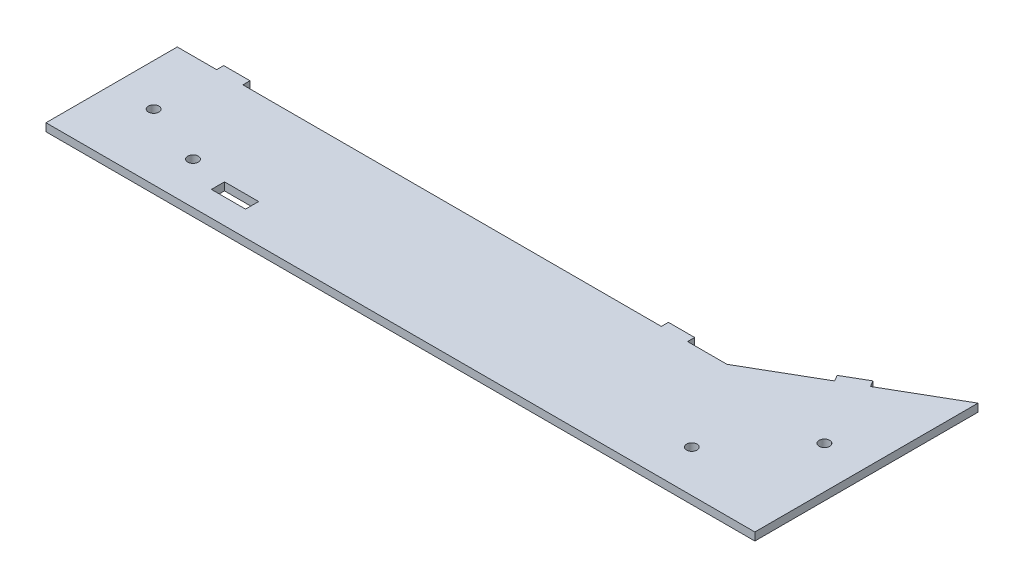
SolidWorks part; units mm, degrees
ref_plane "Front" through (0, 0, 0) normal (0, 0, 1) x (1, 0, 0)
ref_plane "Top" through (0, 0, 0) normal (0, 1, 0) x (1, 0, 0)
ref_plane "Right" through (0, 0, 0) normal (1, 0, 0) x (0, 0, -1)
sketch "Sketch1" plane through (0, 0, 0) normal (0, 1, 0) x (1, 0, 0)
  line L0 (101.1243, 11.2137) -> (101.1243, 66.2733)
  line L1 (40.5025, 31.2733) -> (-168.8757, 31.2733)
  line L2 (101.1243, 11.2137) -> (101.1243, -18.7267)
  line L3 (101.1243, -18.7267) -> (-168.8757, -18.7267)
  line L4 (-168.8757, 31.2733) -> (-168.8757, -18.7267)
  line L5 (101.1243, 11.2137) -> (-168.8757, -18.7267) construction
  line L6 (101.1243, -18.7267) -> (-168.8757, 31.2733) construction
  line L7 (101.1243, 66.2733) -> (40.5025, 31.2733)
  point P0 (0, 0)
  dimension "D1" = 50
  dimension "D2" = 270
  dimension "D3" = 70
  dimension "D4" = 30
  dimension "D5" = 40.5025
extrude "Boss-Extrude1" add sketch "Sketch1" along normal blind 3 contours L1 L4 L3 L2 L0 L7
sketch "Sketch2" plane through (0, 3, 0) normal (0, 1, 0) x (1, 0, 0)
  line L0 (-168.8757, 31.2733) -> (-168.8757, -18.7267) construction
  line L2 (101.1243, 66.2733) -> (101.1243, -18.7267) construction
  circle A0 centre (-152.8757, 6.2733) radius 2
  circle A1 centre (85.1243, 23.7733) radius 2
  point P5 (-168.8757, 6.2733)
  point P9 (101.1243, 23.7733)
  dimension "D1" = 4
  dimension "D3" = 4
  dimension "D2" = 16
  dimension "D4" = 16
extrude "Cut-Extrude1" cut sketch "Sketch2" against normal up to next
sketch "Sketch3" plane through (0, 3, 0) normal (0, 1, 0) x (1, 0, 0)
  line L0 (101.1243, -18.7267) -> (-168.8757, -18.7267) construction
  line L2 (-168.8757, 31.2733) -> (-168.8757, -18.7267) construction
  line L3 (101.1243, 66.2733) -> (101.1243, -18.7267) construction
  circle A0 centre (-128.8757, -2.7267) radius 2
  circle A1 centre (61.1243, -2.7267) radius 2
  dimension "D1" = 4
  dimension "D4" = 4
  dimension "D2" = 40
  dimension "D3" = 16
  dimension "D5" = 16
  dimension "D6" = 40
extrude "Cut-Extrude2" cut sketch "Sketch3" against normal up to next
sketch "Sketch4" plane through (0, 0, -31.2733) normal (0, 0, 1) x (1, 0, 0)
  line L0 (40.5025, 3) -> (-168.8757, 3) construction
  line L1 (-143.8757, 3) -> (-153.8757, 3)
  line L2 (-143.8757, 3) -> (-143.8757, 0)
  line L3 (-143.8757, 0) -> (-153.8757, 0)
  line L4 (-153.8757, 3) -> (-153.8757, 0)
  line L5 (40.5025, 0) -> (-168.8757, 0) construction
  line L6 (-168.8757, 3) -> (-168.8757, 0) construction
  line L7 (25.5025, 3) -> (15.5025, 3)
  line L8 (25.5025, 3) -> (25.5025, 0)
  line L9 (25.5025, 0) -> (15.5025, 0)
  line L10 (15.5025, 3) -> (15.5025, 0)
  line L12 (40.5025, 3) -> (40.5025, 0) construction
  point P14 (-168.8757, 1.5)
  point P17 (40.5025, 1.5)
  dimension "D1" = 10
  dimension "D2" = 10
  dimension "D3" = 15
  dimension "D4" = 15
extrude "Boss-Extrude3" add sketch "Sketch4" against normal blind 2.7
sketch "Sketch5" plane through (-3.4161, 0, -5.9168) normal (-0.5, 0, -0.866) x (-0.866, 0, 0.5)
  line L0 (-120.7129, 3) -> (-50.7129, 3) construction
  line L1 (-90.7129, 3) -> (-80.7129, 3)
  line L2 (-90.7129, 3) -> (-90.7129, 0)
  line L3 (-90.7129, 0) -> (-80.7129, 0)
  line L4 (-80.7129, 3) -> (-80.7129, 0)
  line L5 (-120.7129, 0) -> (-50.7129, 0) construction
  point P8 (-85.7129, 3)
  point P9 (-85.7129, 3)
  dimension "D1" = 10
extrude "Boss-Extrude4" add sketch "Sketch5" along normal blind 2.7
sketch "Sketch6" plane through (0, 3, 0) normal (0, 1, 0) x (1, 0, 0)
  line L0 (101.1243, -18.7267) -> (-168.8757, -18.7267) construction
  line L1 (-115.3757, -4.2267) -> (-102.3757, -4.2267)
  line L2 (-115.3757, -4.2267) -> (-115.3757, -9.2267)
  line L3 (-115.3757, -9.2267) -> (-102.3757, -9.2267)
  line L4 (-102.3757, -4.2267) -> (-102.3757, -9.2267)
  line L5 (-115.3757, -4.2267) -> (-102.3757, -9.2267) construction
  line L6 (-115.3757, -9.2267) -> (-102.3757, -4.2267) construction
  line L7 (-168.8757, 31.2733) -> (-168.8757, -18.7267) construction
  point P0 (-108.8757, -6.7267)
  dimension "D1" = 13
  dimension "D2" = 5
  dimension "D3" = 12
  dimension "D4" = 60
extrude "Cut-Extrude3" cut sketch "Sketch6" against normal up to next
